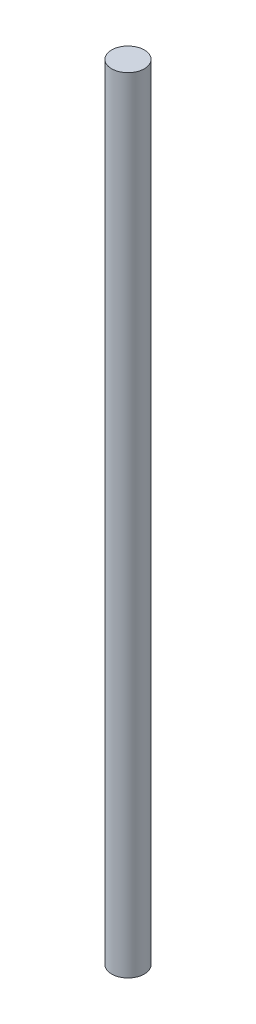
SolidWorks part; units mm, degrees
material "ABS"
ref_plane "Front Plane" through (0, 0, 0) normal (0, 0, 1) x (1, 0, 0)
ref_plane "Top Plane" through (0, 0, 0) normal (0, 1, 0) x (1, 0, 0)
ref_plane "Right Plane" through (0, 0, 0) normal (1, 0, 0) x (0, 0, -1)
sketch "Sketch1" plane through (0, 0, 0) normal (0, 1, 0) x (1, 0, 0)
  circle A0 centre (0, 0) radius 2.5
extrude "Boss-Extrude1" add sketch "Sketch1" along normal blind 120
